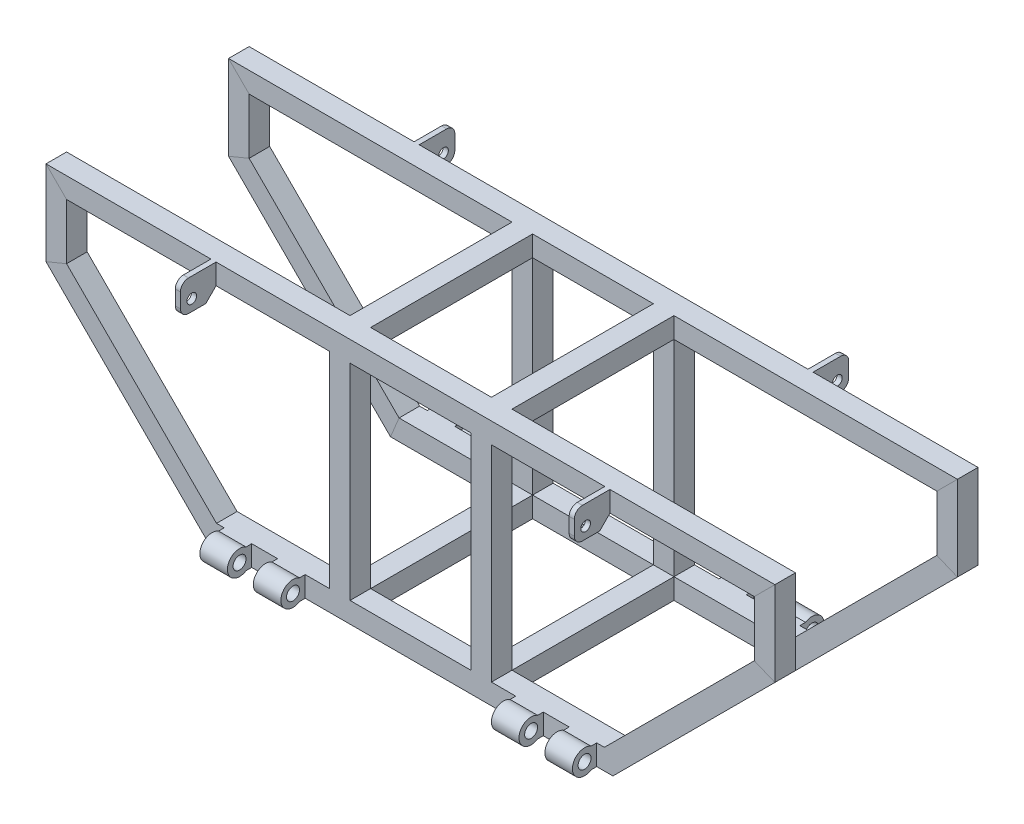
SolidWorks part; units mm, degrees
material "Ductile Iron (SN)"
ref_plane "Front Plane" through (0, 0, 0) normal (0, 0, 1) x (1, 0, 0)
ref_plane "Top Plane" through (0, 0, 0) normal (0, 1, 0) x (1, 0, 0)
ref_plane "Right Plane" through (0, 0, 0) normal (1, 0, 0) x (0, 0, -1)
ref_plane "Botton Plane" through (0, -355.4, 0) normal (0, 1, 0) x (1, 0, 0)
sketch "Sketch8" plane through (0, 0, 0) normal (1, 0, 0) x (0, 0, -1)
  line L0 (-124.2, -305.8) -> (-124.2, -328.8)
  line L1 (-125.4, -304.6) -> (-100, -304.6)
  line L2 (-125.4, -304.6) -> (-125.4, -330)
  line L3 (-125.4, -330) -> (-100, -330)
  line L4 (-100, -304.6) -> (-100, -330)
  line L5 (0, 0) -> (0, -355.4) construction
  line L6 (467.5, -355.4) -> (-467.5, -355.4) construction
  line L7 (-124.2, -328.8) -> (-101.2, -328.8)
  line L8 (-101.2, -305.8) -> (-101.2, -328.8)
  line L9 (-124.2, -305.8) -> (-101.2, -305.8)
  point P12 (0, 0)
  dimension "D1" = 25.4
  dimension "D2" = 25.4
  dimension "D4" = 100
  dimension "D5" = 25.4
  dimension "D3" = 1.2
sketch "Sketch9" plane through (0, 0, 0) normal (0, 0, 1) x (1, 0, 0)
  line L0 (-450, -130) -> (-250, -330)
  line L2 (-450, -25.4) -> (-450, -130)
  line L3 (-250, -330) -> (250, -330)
  line L4 (450, -25.4) -> (450, -130)
  line L5 (450, -130) -> (250, -330)
  line L7 (-36.122, -355.4) -> (36.122, -355.4) construction
  line L8 (-450, -25.4) -> (450, -25.4)
  line L9 (467.5, -355.4) -> (-467.5, -355.4) construction
  line L10 (-450, 0) -> (450, 0) construction
  point P3 (0, 0)
  point P12 (0, 0)
  point P13 (0, 0)
  point P16 (0, 0)
  point P17 (0, -355.4)
  dimension "D4" = 45
  dimension "D1" = 900
  dimension "D3" = 200
  dimension "D5" = 45
  dimension "D6" = 200
  dimension "D2" = 330
  dimension "D8" = 25.4
sweep "Sweep3" add profiles "Sketch8" path "Sketch9"
ref_plane "Plane2" through (-110, 0, 0) normal (-1, 0, 0) x (0, 0, 1)
sketch "Sketch10" plane through (-110, 0, 0) normal (-1, 0, 0) x (0, 0, 1)
  line L0 (125.4, -330) -> (125.4, -304.6) construction
  line L2 (125.4, -304.6) -> (132.4181, -304.6)
  line L5 (132.4181, -330) -> (125.4, -330)
  line L6 (125.4, -330) -> (125.4, -304.6)
  arc A0 (132.4181, -330) -> (132.4181, -304.6) centre (140.4, -317.3) ccw
  circle A1 centre (140.4, -317.3) radius 8
  point P1 (0, 0)
  point P2 (0, 0)
  point P3 (125.4, -317.3)
  point P4 (0, 0)
  point P10 (0, 0)
  point P11 (0, 0)
  dimension "D1" = 30
  dimension "D2" = 16
extrude "Boss-Extrude2" add sketch "Sketch10" along normal blind 140
sketch "Sketch11" plane through (0, -355.4, 0) normal (0, 1, 0) x (1, 0, 0)
  line L0 (250, -125.4) -> (-110, -125.4) construction
  line L1 (-110, -125.4) -> (-164, -125.4) construction
  line L2 (-110, -125.4) -> (-110, -155.4) construction
  line L3 (-110, -155.4) -> (-164, -155.4) construction
  line L4 (-164, -125.4) -> (-164, -155.4) construction
  line L6 (-196, -125.4) -> (-250, -125.4) construction
  line L7 (-196, -125.4) -> (-196, -155.4) construction
  line L8 (-196, -155.4) -> (-250, -155.4) construction
  line L9 (-250, -125.4) -> (-250, -155.4) construction
  line L10 (-110, 186.614) -> (-110, -186.614) construction
  line L11 (-250, -125.4) -> (-250, -132.4181) construction
  line L13 (-164, -125.4) -> (-196, -125.4)
  line L14 (-164, -125.4) -> (-164, -155.4)
  line L15 (-164, -155.4) -> (-196, -155.4)
  line L16 (-196, -125.4) -> (-196, -155.4)
  line L17 (-110, -125.4) -> (-130, -125.4)
  line L18 (-110, -125.4) -> (-110, -155.4)
  line L19 (-110, -155.4) -> (-130, -155.4)
  line L20 (-130, -125.4) -> (-130, -155.4)
  line L21 (-250, -125.4) -> (-230, -125.4)
  line L22 (-250, -125.4) -> (-250, -155.4)
  line L23 (-250, -155.4) -> (-230, -155.4)
  line L24 (-230, -125.4) -> (-230, -155.4)
  dimension "D1" = 54
  dimension "D2" = 30
  dimension "D3" = 20
  dimension "D4" = 20
extrude "Cut-Extrude1" cut sketch "Sketch11" against normal blind 5 and the other way blind 80
ref_plane "Plane3" through (110, 0, 0) normal (1, 0, 0) x (0, 0, -1)
sketch "Sketch12" plane through (110, 0, 0) normal (1, 0, 0) x (0, 0, -1)
  line L2 (-125.4, -304.6) -> (-132.4181, -304.6)
  line L3 (-125.4, -304.6) -> (-125.4, -330)
  line L5 (-125.4, -330) -> (-132.4181, -330)
  line L6 (-125.4, -304.6) -> (-125.4, -330) construction
  line L7 (-125.4, -304.6) -> (-125.4, -330) construction
  arc A0 (-132.4181, -304.6) -> (-132.4181, -330) centre (-140.4, -317.3) ccw
  circle A1 centre (-140.4, -317.3) radius 8
  point P1 (0, 0)
  point P6 (0, 0)
  point P7 (-125.4, -317.3)
  point P8 (0, 0)
  point P12 (-130.1913, -326.5802)
  point P14 (0, 0)
  dimension "D1" = 16
  dimension "D2" = 30
extrude "Boss-Extrude3" add sketch "Sketch12" along normal blind 140
sketch "Sketch13" plane through (0, -355.4, 0) normal (0, 1, 0) x (1, 0, 0)
  line L0 (110, -125.4) -> (-130, -125.4) construction
  line L1 (250, -125.4) -> (230, -125.4)
  line L2 (250, -125.4) -> (250, -155.4)
  line L3 (250, -155.4) -> (230, -155.4)
  line L4 (230, -125.4) -> (230, -155.4)
  line L5 (196, -125.4) -> (164, -125.4)
  line L6 (196, -125.4) -> (196, -155.4)
  line L7 (196, -155.4) -> (164, -155.4)
  line L8 (164, -125.4) -> (164, -155.4)
  line L9 (110, -132.4181) -> (110, -125.4) construction
  line L10 (130, -125.4) -> (110, -125.4)
  line L11 (130, -125.4) -> (130, -155.4)
  line L12 (130, -155.4) -> (110, -155.4)
  line L13 (110, -125.4) -> (110, -155.4)
  line L16 (250, -125.4) -> (250, -132.4181) construction
  point P10 (0, 0)
  dimension "D1" = 30
  dimension "D2" = 20
  dimension "D3" = 54
  dimension "D4" = 54
extrude "Cut-Extrude2" cut sketch "Sketch13" against normal blind 11 and the other way blind 66
sketch "Sketch18" plane through (0, 0, 100) normal (0, 0, -1) x (-1, 0, 0)
  line L0 (450, -25.4) -> (-450, -25.4) construction
  line L1 (-100, -50.8) -> (-74.6, -50.8)
  line L2 (-100, -50.8) -> (-100, -25.4)
  line L3 (-100, -25.4) -> (-74.6, -25.4)
  line L4 (-74.6, -50.8) -> (-74.6, -25.4)
  line L6 (74.6, -50.8) -> (100, -50.8)
  line L7 (74.6, -50.8) -> (74.6, -25.4)
  line L8 (74.6, -25.4) -> (100, -25.4)
  line L9 (100, -50.8) -> (100, -25.4)
  line L10 (-100, -304.6) -> (-74.6, -304.6)
  line L11 (-100, -304.6) -> (-100, -330)
  line L12 (-100, -330) -> (-74.6, -330)
  line L13 (-74.6, -304.6) -> (-74.6, -330)
  line L14 (75.8, -305.8) -> (75.8, -328.8)
  line L15 (74.6, -304.6) -> (100, -304.6)
  line L16 (74.6, -304.6) -> (74.6, -330)
  line L17 (74.6, -330) -> (100, -330)
  line L18 (100, -304.6) -> (100, -330)
  line L19 (75.8, -328.8) -> (98.8, -328.8)
  line L20 (98.8, -305.8) -> (98.8, -328.8)
  line L21 (75.8, -305.8) -> (98.8, -305.8)
  line L22 (-98.8, -305.8) -> (-98.8, -328.8)
  line L23 (-98.8, -328.8) -> (-75.8, -328.8)
  line L24 (-75.8, -305.8) -> (-75.8, -328.8)
  line L25 (-98.8, -305.8) -> (-75.8, -305.8)
  line L26 (-98.8, -49.6) -> (-75.8, -49.6)
  line L27 (-75.8, -49.6) -> (-75.8, -26.6)
  line L28 (-98.8, -26.6) -> (-75.8, -26.6)
  line L29 (-98.8, -49.6) -> (-98.8, -26.6)
  line L30 (98.8, -49.6) -> (98.8, -26.6)
  line L31 (75.8, -26.6) -> (98.8, -26.6)
  line L32 (75.8, -49.6) -> (75.8, -26.6)
  line L33 (75.8, -49.6) -> (98.8, -49.6)
  line L34 (0, 0) -> (0, -330) construction
  line L35 (-250, -330) -> (250, -330) construction
  line L36 (424.6, -50.8) -> (-424.6, -50.8) construction
  point P40 (0, 0)
  point P46 (0, 0)
  point P47 (0, 0)
  point P48 (0, 0)
  point P50 (-134.8641, -12.5007)
  dimension "D2" = 25.4
  dimension "D3" = 100
  dimension "D4" = 100
  dimension "D1" = 1.2
extrude "Boss-Extrude8" add sketch "Sketch18" along normal up to surface (100 mm away) up to plane "Front Plane"
sketch "Sketch17" plane through (0, -304.6, 0) normal (0, 1, 0) x (1, 0, 0)
  line L0 (130, -125.4) -> (-130, -125.4) construction
  line L1 (-100, -125.4) -> (-74.6, -125.4)
  line L2 (-100, -125.4) -> (-100, -100)
  line L3 (-100, -100) -> (-74.6, -100)
  line L4 (-74.6, -125.4) -> (-74.6, -100)
  line L5 (239.479, -100) -> (100, -100) construction
  line L6 (-112.0372, 0) -> (112.0372, 0) construction
  line L7 (74.6, -125.4) -> (100, -125.4)
  line L8 (74.6, -125.4) -> (74.6, -100)
  line L9 (74.6, -100) -> (100, -100)
  line L10 (100, -125.4) -> (100, -100)
  line L11 (0, 173.4515) -> (0, -173.4515) construction
  line L12 (-98.8, -124.2) -> (-98.8, -101.2)
  line L13 (-98.8, -101.2) -> (-75.8, -101.2)
  line L14 (-75.8, -124.2) -> (-75.8, -101.2)
  line L15 (-98.8, -124.2) -> (-75.8, -124.2)
  line L16 (75.8, -124.2) -> (75.8, -101.2)
  line L17 (75.8, -101.2) -> (98.8, -101.2)
  line L18 (98.8, -124.2) -> (98.8, -101.2)
  line L19 (75.8, -124.2) -> (98.8, -124.2)
  line L20 (98.8, 124.2) -> (98.8, 101.2)
  line L21 (75.8, 101.2) -> (98.8, 101.2)
  line L22 (75.8, 124.2) -> (75.8, 101.2)
  line L23 (-98.8, 124.2) -> (-75.8, 124.2)
  line L24 (-75.8, 124.2) -> (-75.8, 101.2)
  line L25 (-98.8, 124.2) -> (-98.8, 101.2)
  line L26 (100, 125.4) -> (100, 100)
  line L27 (74.6, 100) -> (100, 100)
  line L28 (74.6, 125.4) -> (74.6, 100)
  line L29 (-74.6, 125.4) -> (-74.6, 100)
  line L30 (-100, 125.4) -> (-100, 100)
  line L31 (-100, 125.4) -> (-74.6, 125.4)
  line L32 (75.8, 124.2) -> (98.8, 124.2)
  line L33 (-98.8, 101.2) -> (-75.8, 101.2)
  line L34 (74.6, 125.4) -> (100, 125.4)
  line L35 (-100, 100) -> (-74.6, 100)
  point P16 (0, 0)
  point P20 (0, 0)
  dimension "D1" = 25.4
  dimension "D2" = 25.4
  dimension "D3" = 100
  dimension "D4" = 100
  dimension "D5" = 1.2
ref_plane "Plane4" through (240, 0, 0) normal (-1, 0, 0) x (0, 0, 1)
mirror "Mirror10" about plane through (0, 0, 0) normal (0, 0, 1) of bodies 126
extrude "Boss-Extrude9" add sketch "Sketch17" along normal up to surface (253.8 mm away)
sketch "Sketch14" plane through (240, 0, 0) normal (-1, 0, 0) x (0, 0, 1)
  line L0 (125.4, -25.4) -> (125.4, -50.8)
  line L5 (125.4, -50.8) -> (138.1, -63.5)
  line L6 (138.1, -63.5) -> (159.4, -63.5)
  line L7 (169.4, -53.5) -> (169.4, -35.4)
  line L8 (159.4, -25.4) -> (125.4, -25.4)
  line L9 (125.4, -50.8) -> (125.4, -304.6) construction
  line L10 (0, 23.9363) -> (0, -36.8197) construction
  line L11 (-159.4, -25.4) -> (-125.4, -25.4)
  line L12 (-169.4, -53.5) -> (-169.4, -35.4)
  line L13 (-138.1, -63.5) -> (-159.4, -63.5)
  line L14 (-125.4, -50.8) -> (-138.1, -63.5)
  line L15 (-125.4, -25.4) -> (-125.4, -50.8)
  circle A0 centre (155.4, -49.5) radius 6
  arc A1 (159.4, -63.5) -> (169.4, -53.5) centre (159.4, -53.5) ccw
  arc A2 (169.4, -35.4) -> (159.4, -25.4) centre (159.4, -35.4) ccw
  arc A3 (-169.4, -35.4) -> (-159.4, -25.4) centre (-159.4, -35.4) cw
  arc A4 (-159.4, -63.5) -> (-169.4, -53.5) centre (-159.4, -53.5) cw
  circle A5 centre (-155.4, -49.5) radius 6
  point P14 (169.4, -63.5)
  point P17 (169.4, -25.4)
  point P31 (-169.4, -25.4)
  point P32 (-169.4, -63.5)
  dimension "D2" = 12
  dimension "D7" = 10
  dimension "D1" = 25.4
  dimension "D3" = 38.1
  dimension "D4" = 30
  dimension "D5" = 14
  dimension "D6" = 135
  dimension "D8" = 14
extrude "Boss-Extrude4" add sketch "Sketch14" against normal blind 6.35
mirror "Mirror11" about plane through (0, 0, 0) normal (1, 0, 0) of "Boss-Extrude4"
equation "\"Length\"= 121cm"
equation "\"Width\"= 90cm"
equation "\"pipeThickness\" = 0.12cm"
equation "\"pipeWidth\" = 2.54cm"
equation "\"D1@Sketch8\"=\"pipeWidth\""
equation "\"D3@Sketch8\"= \"pipeThickness\""
equation "\"Height\" = 33cm"
equation "\"D2@Sketch8\"= \"pipeWidth\""
equation "\"D1@Sketch17\"=\"pipeWidth\""
equation "\"D2@Sketch17\"=\"pipeWidth\""
equation "\"D5@Sketch17\"=\"pipeThickness\""
equation "\"D5@Sketch8\"=\"pipeWidth\""
equation "\"D8@Sketch9\"=\"pipeWidth\""
